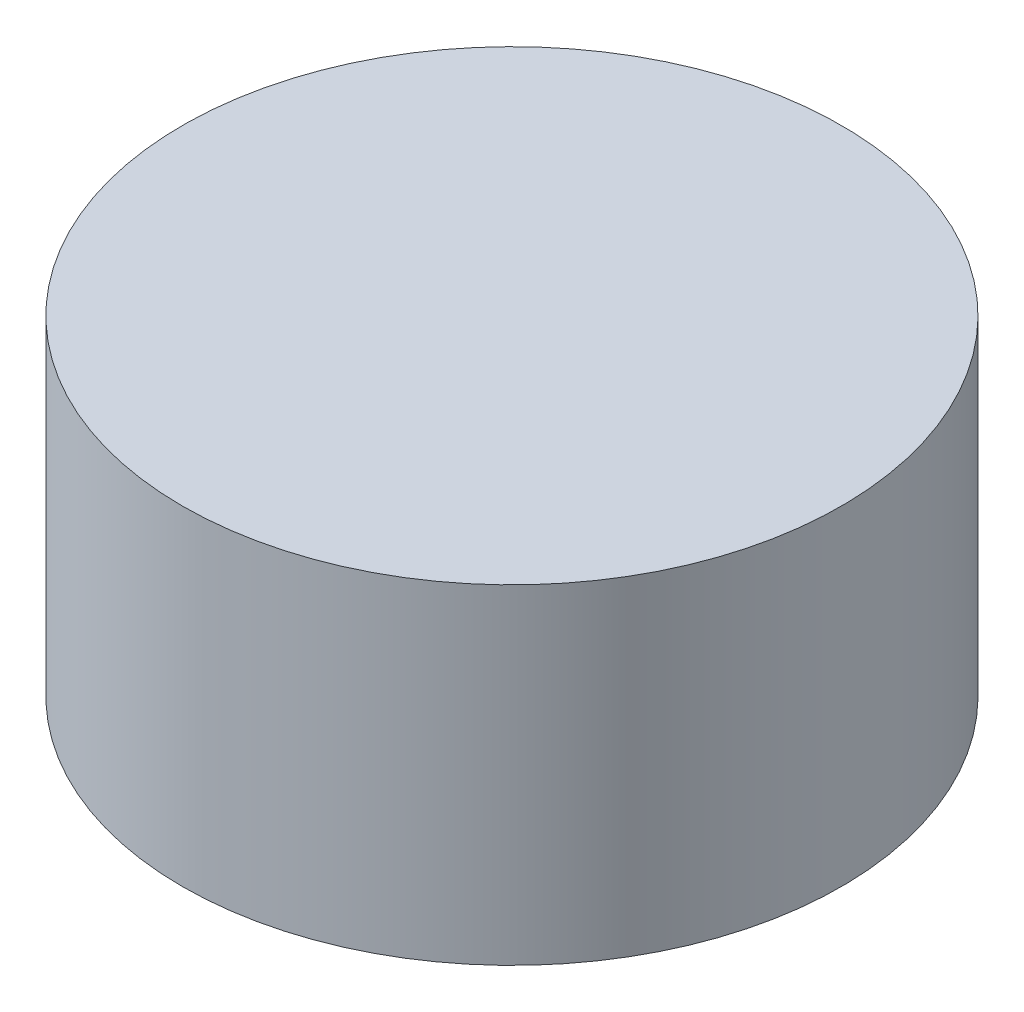
SolidWorks part; units mm, degrees
ref_plane "Front Plane" through (0, 0, 0) normal (0, 0, 1) x (1, 0, 0)
ref_plane "Top Plane" through (0, 0, 0) normal (0, 1, 0) x (1, 0, 0)
ref_plane "Right Plane" through (0, 0, 0) normal (1, 0, 0) x (0, 0, -1)
sketch "Sketch1" plane through (0, 0, 0) normal (0, 1, 0) x (1, 0, 0)
  circle A0 centre (0, 0) radius 50
extrude "Boss-Extrude1" add sketch "Sketch1" along normal blind 50
